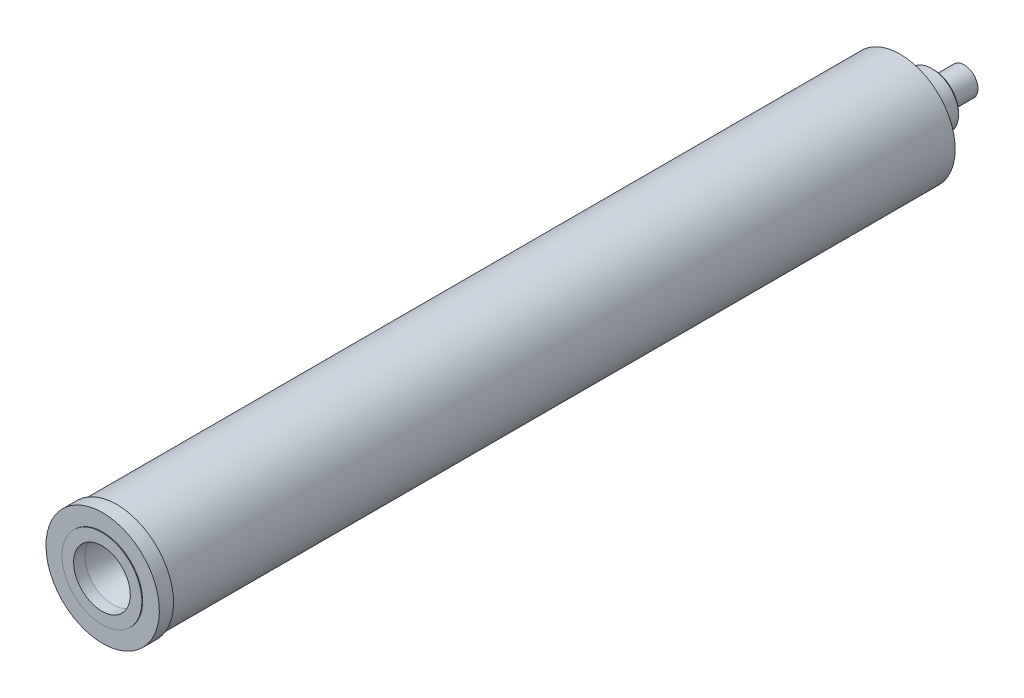
SolidWorks part; units mm, degrees
material "6061-T6 (SS)"
ref_plane "Front Plane" through (0, 0, 0) normal (0, 0, 1) x (1, 0, 0)
ref_plane "Top Plane" through (0, 0, 0) normal (0, 1, 0) x (1, 0, 0)
ref_plane "Right Plane" through (0, 0, 0) normal (1, 0, 0) x (0, 0, -1)
sketch "Sketch1" plane through (0, 0, 0) normal (1, 0, 0) x (0, 0, -1)
  line L0 (-420.878, 50.8) -> (-408.178, 50.8)
  line L1 (-408.178, 50.8) -> (-408.178, 49.2125)
  line L2 (-408.178, 49.2125) -> (293.878, 49.2125)
  line L3 (293.878, 49.2125) -> (293.878, 23.876)
  line L4 (271.028, 0) -> (351.028, 0)
  line L5 (271.028, 0) -> (271.028, 29.25)
  line L6 (271.028, 29.25) -> (-301.513, 29.25)
  line L7 (-301.513, 29.25) -> (-301.513, 40.25)
  line L8 (-301.513, 40.25) -> (-309.5068, 40.25)
  line L9 (-309.5068, 40.25) -> (-336.513, 13.2438)
  line L10 (-351.513, 14.8204) -> (-336.513, 13.2438)
  line L11 (-351.513, 14.8204) -> (-411.513, 25.4)
  line L12 (-411.513, 25.4) -> (-421.513, 25.4)
  line L13 (-420.878, 50.8) -> (-420.878, 35.8)
  line L14 (473.12, 0) -> (-433.5179, 0) construction
  line L15 (293.878, 23.876) -> (323.723, 23.876)
  line L16 (323.723, 23.876) -> (323.723, 12.5)
  line L17 (323.723, 12.5) -> (351.028, 12.5)
  line L18 (351.028, 12.5) -> (351.028, 0)
  line L19 (-420.878, 35.8) -> (-421.513, 35.8)
  line L20 (-421.513, 35.8) -> (-421.513, 25.4)
  point P1 (323.723, 18.188)
  point P25 (351.028, 6.25)
  dimension "D2" = 702.056
  dimension "D3" = 49.2125
  dimension "D4" = 6
  dimension "D5" = 10
  dimension "D6" = 60
  dimension "D7" = 57.15
  dimension "D8" = 29.845
  dimension "D9" = 135
  dimension "D10" = 23.876
  dimension "D11" = 12.5
  dimension "D12" = 12.7
  dimension "D13" = 35
  dimension "D14" = 15
  dimension "D15" = 10
  dimension "D16" = 50.8
  dimension "D17" = 25.4
  dimension "D18" = 0.635
  dimension "D19" = 15
  dimension "D20" = 29.25
  dimension "D21" = 351.028
  dimension "D22" = 11
  dimension "D23" = 80
revolve "Revolve1" add sketch "Sketch1" angle 360 about L14
chamfer "Chamfer1" distance 1.5 angle 45 1 edges at (0, 23.876, -323.723)
hole_wizard "3/8-16 Tapped Hole1" positions "Sketch2" profile "Sketch4" tap size "3/8-16" standard "ANSI Inch"
sketch "Sketch2" plane through (0, 0, -351.028) normal (0, 0, -1) x (-1, 0, 0)
  point P0 (0, 0)
sketch "Sketch4" plane through (0, 0, -351.028) normal (1, 0, 0) x (0, 1, 0)
  line L0 (0, 0) -> (0, 27.7847)
  line L1 (0, 27.7847) -> (3.9687, 25.4)
  line L2 (3.9687, 25.4) -> (3.9687, 1.1989)
  line L3 (3.9687, 1.1989) -> (5.3975, 0)
  line L5 (5.3975, 0) -> (0, 0)
  line L6 (-3.9687, 1.1989) -> (-5.3975, 0) construction
  line L10 (0, 27.7847) -> (-3.9688, 25.4) construction
  line L11 (0, -6.35) -> (0, 107.95) construction
  dimension "Tap Drill Dia." = 7.9375
  dimension "Tap Drill Depth" = 25.4
  dimension "Near C'Sink Dia." = 10.795
  dimension "Near C'Sink Angle" = 100
  dimension "Drill Angle" = 118
cosmetic thread "Hole Thread1" parameters "D1"=19.05, "D2"=9.525
